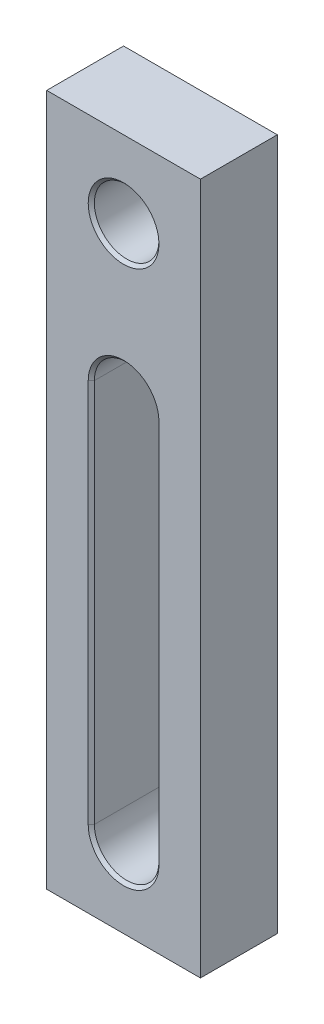
SolidWorks part; units mm, degrees
material "Простая углеродистая сталь"
ref_plane "Спереди" through (0, 0, 0) normal (0, 0, 1) x (1, 0, 0)
ref_plane "Сверху" through (0, 0, 0) normal (0, 1, 0) x (1, 0, 0)
ref_plane "Справа" through (0, 0, 0) normal (1, 0, 0) x (0, 0, -1)
sketch "Эскиз1" plane through (0, 0, 0) normal (0, 0, 1) x (1, 0, 0)
  line L1 (0, 0) -> (50, 0)
  line L2 (0, 0) -> (0, 225)
  line L3 (0, 225) -> (50, 225)
  line L4 (50, 0) -> (50, 225)
  dimension "D1" = 50
  dimension "D2" = 225
extrude "Бобышка-Вытянуть1" add sketch "Эскиз1" along normal blind 25
sketch "Эскиз2" plane through (0, 0, 25) normal (0, 0, 1) x (1, 0, 0)
  line L1 (14.5, 25) -> (14.5, 150)
  line L2 (35.5, 25) -> (35.5, 150)
  line L3 (0, 225) -> (0, 0) construction
  line L4 (0, 0) -> (50, 0) construction
  arc A0 (14.5, 25) -> (35.5, 25) centre (25, 25) ccw
  arc A1 (14.5, 150) -> (35.5, 150) centre (25, 150) cw
  circle A2 centre (25, 200) radius 10.5
  point P7 (14.5, 87.5)
  point P10 (35.5, 87.5)
  dimension "D1" = 25
  dimension "D2" = 25
  dimension "D3" = 21
  dimension "D4" = 21
extrude "Вырез-Вытянуть1" cut sketch "Эскиз2" against normal through all
chamfer "Фаска1" distance 1 angle 45 10 edges at (14.5, 87.5, 0) (25, 14.5, 0) (25, 160.5, 0) (35.5, 87.5, 0) (35.5, 87.5, 25) (25, 160.5, 25) (25, 14.5, 25) (14.5, 87.5, 25) (35.5, 200, 0) (35.5, 200, 25)
